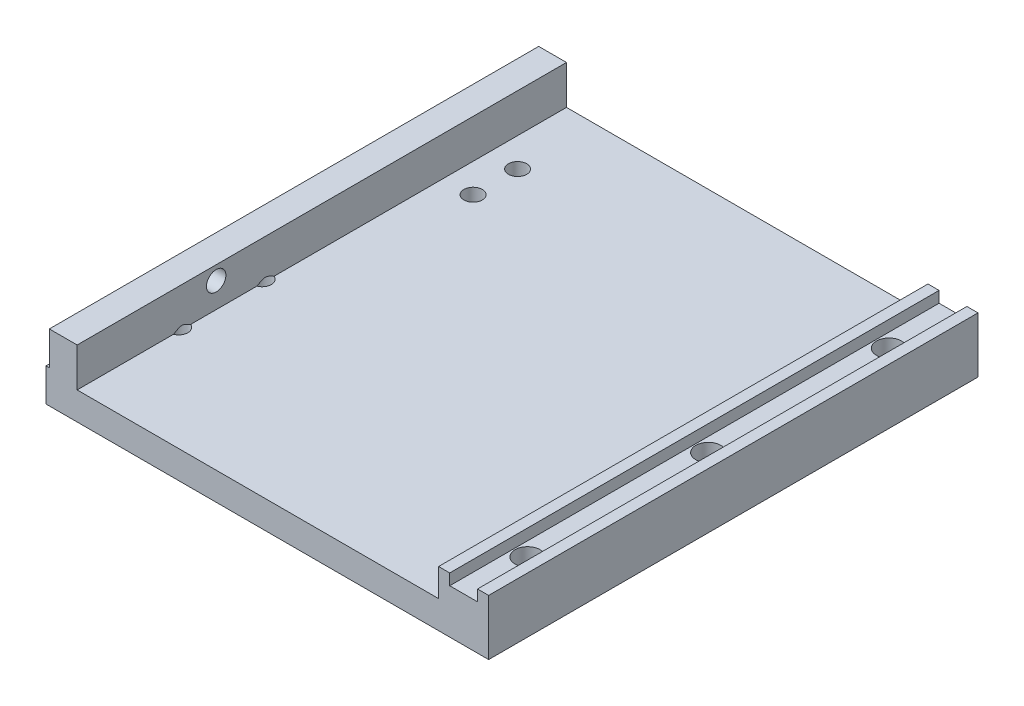
SolidWorks part; units mm, degrees
ref_plane "前视基准面" through (0, 0, 0) normal (0, 0, 1) x (1, 0, 0)
ref_plane "上视基准面" through (0, 0, 0) normal (0, 1, 0) x (1, 0, 0)
ref_plane "右视基准面" through (0, 0, 0) normal (1, 0, 0) x (0, 0, -1)
sketch "草图1" plane through (0, 0, 0) normal (0, 0, 1) x (1, 0, 0)
  line L0 (-9, 10) -> (-9, 5)
  line L1 (-9, 10) -> (-7, 10)
  line L2 (-7, 10) -> (-7, 8)
  line L3 (-7, 8) -> (-2, 8)
  line L4 (-2, 8) -> (-2, 10)
  line L5 (-2, 10) -> (0, 10)
  line L6 (0, 10) -> (0, 0)
  line L7 (-79.6, 0) -> (-79.6, 5.9)
  line L8 (-79.6, 5.9) -> (-79, 5.9)
  line L9 (-79, 5.9) -> (-79, 12)
  line L10 (-74, 12) -> (-79, 12)
  line L11 (-74, 12) -> (-74, 5)
  line L12 (-9, 5) -> (-74, 5)
  line L13 (0, 0) -> (-79.6, 0)
  line L21 (-0.5, 0) -> (-0.5, 4.4) construction
  line L22 (-8.5, 4.4) -> (-8.5, 0) construction
  line L24 (-6.75, 8) -> (-6.75, 4.4) construction
  line L30 (-74, 11.25) -> (-79, 11.25) construction
extrude "凸台-拉伸1" add sketch "草图1" along normal blind 88
hole_wizard "M4 六角凹头螺钉的柱形沉头孔1" positions "草图2" profile "草图3" counterbore size "M4" standard "ISO" end condition through all
sketch "草图2" plane through (0, 0, 0) normal (0, -1, 0) x (-1, 0, 0)
  line L0 (79.6, -44) -> (-18.4609, -44) construction
  line L1 (79.6, -88) -> (79.6, 0) construction
  line L3 (0, -88) -> (0, 0) construction
  point P0 (4.5, -11.5)
  point P2 (4.5, -44)
  point P4 (4.5, -76.5)
  dimension "D1" = 65
  dimension "D2" = 4.5
sketch "草图3" plane through (-4.5, 0, 11.5) normal (1, 0, 0) x (0, 0, -1)
  line L0 (0, 0) -> (0, 12)
  line L1 (0, 12) -> (2.25, 12)
  line L3 (2.25, 12) -> (2.25, 4.4)
  line L4 (2.25, 4.4) -> (4, 4.4)
  line L5 (4, 4.4) -> (4, 0)
  line L7 (4, 0) -> (0, 0)
  line L11 (0, -6.35) -> (0, 107.95) construction
  dimension "通孔孔直径" = 4.5
  dimension "通孔孔深度" = 12
  dimension "柱形沉头孔直径" = 8
  dimension "柱形沉头孔深度" = 4.4
hole_wizard "M4 螺纹孔1" positions "草图4" profile "草图5" tap size "M4" standard "ISO" end condition through all
sketch "草图4" plane through (0, 0, 0) normal (0, -1, 0) x (-1, 0, 0)
  line L0 (0, -88) -> (0, 0) construction
  line L1 (79.6, 0) -> (0, 0) construction
  point P0 (68.8, -14)
  point P2 (68.8, -22)
  dimension "D1" = 68.8
  dimension "D2" = 14
  dimension "D3" = 22
sketch "草图5" plane through (-68.8, 0, 14) normal (1, 0, 0) x (0, 0, -1)
  line L0 (0, 0) -> (0, 12)
  line L1 (0, 12) -> (1.65, 12)
  line L2 (1.65, 12) -> (1.65, 0)
  line L5 (1.65, 0) -> (0, 0)
  line L11 (0, -6.35) -> (0, 107.95) construction
  dimension "通孔螺纹孔钻头直径" = 3.3
  dimension "通孔螺纹孔钻头深度" = 12
cosmetic thread "孔螺蚊线1" parameters "D2"=4
cosmetic thread "孔螺蚊线2" parameters "D2"=4
hole_wizard "M3 螺纹孔1" positions "草图6" profile "草图7" tap size "M3" standard "ISO"
sketch "草图6" plane through (-79.6, 0, 0) normal (-1, 0, 0) x (0, 0, 1)
  line L0 (44, 5.9) -> (44, -5.3544) construction
  line L1 (88, 5.9) -> (0, 5.9) construction
  line L4 (88, 0) -> (0, 0) construction
  point P0 (11.5, 3)
  point P2 (44, 3)
  point P4 (76.5, 3)
  dimension "D1" = 65
  dimension "D2" = 3
cosmetic thread "孔螺蚊线3" parameters "D1"=8, "D2"=3
cosmetic thread "孔螺蚊线4" parameters "D1"=8, "D2"=3
cosmetic thread "孔螺蚊线5" parameters "D1"=8, "D2"=3
sketch "草图7" plane through (-79.6, 3, 11.5) normal (0, 1, 0) x (0, 0, 1)
  line L0 (0, 0) -> (0, 10.2511)
  line L1 (0, 10.2511) -> (1.25, 9.5)
  line L2 (1.25, 9.5) -> (1.25, 0)
  line L5 (1.25, 0) -> (0, 0)
  line L10 (0, 10.2511) -> (-1.25, 9.5) construction
  line L11 (0, -6.35) -> (0, 107.95) construction
  dimension "螺纹孔钻头直径" = 2.5
  dimension "螺纹孔钻头深度" = 9.5
  dimension "导头角度" = 118
sketch "草图8" plane through (-79, 0, 0) normal (-1, 0, 0) x (0, 0, 1)
  line L0 (88, 12) -> (0, 12) construction
  line L1 (0, 12) -> (0, 5.9) construction
  circle A0 centre (63, 9.5) radius 1.75
  dimension "D1" = 3.5
  dimension "D2" = 2.5
  dimension "D3" = 63
extrude "切除-拉伸1" cut sketch "草图8" against normal blind 5
sketch "草图9" plane through (0, 5.9, 0) normal (0, 1, 0) x (1, 0, 0)
  line L1 (-79.6, -88) -> (-79, -88)
  line L2 (-79.6, -88) -> (-79.6, 0)
  line L3 (-79.6, 0) -> (-79, 0)
  line L4 (-79, -88) -> (-79, 0)
extrude "凸台-拉伸2" add sketch "草图9" along normal blind 0.05
hole_wizard "M4 螺纹孔2" positions "草图10" profile "草图11" tap size "M4" standard "ISO"
sketch "草图10" plane through (0, 0, 0) normal (0, -1, 0) x (-1, 0, 0)
  point P0 (74.6, -54.1418)
  point P3 (74.6, -69.1418)
sketch "草图11" plane through (-74.6, 0, 54.1418) normal (1, 0, 0) x (0, 0, -1)
  line L0 (0, 0) -> (0, 5.9914)
  line L1 (0, 5.9914) -> (1.65, 5)
  line L2 (1.65, 5) -> (1.65, 0)
  line L5 (1.65, 0) -> (0, 0)
  line L10 (0, 5.9914) -> (-1.65, 5) construction
  line L11 (0, -6.35) -> (0, 107.95) construction
  dimension "螺纹孔钻头直径" = 3.3
  dimension "螺纹孔钻头深度" = 5
  dimension "导头角度" = 118
cosmetic thread "孔螺蚊线6" parameters "D1"=5, "D2"=4
cosmetic thread "孔螺蚊线7" parameters "D1"=5, "D2"=4
